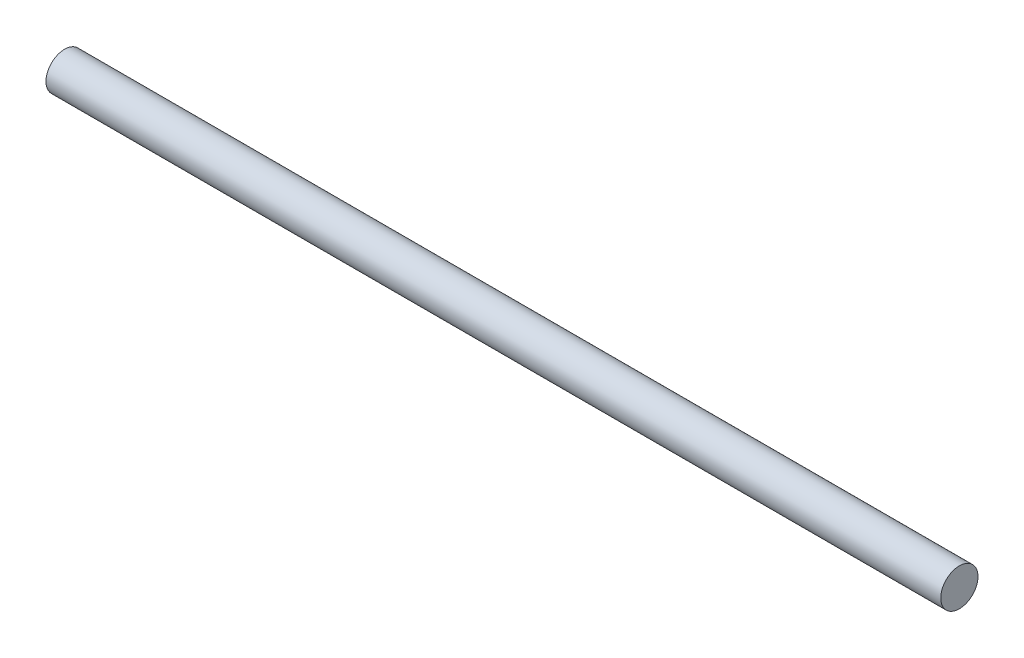
SolidWorks part; units mm, degrees
ref_plane "Front Plane" through (0, 0, 0) normal (0, 0, 1) x (1, 0, 0)
ref_plane "Top Plane" through (0, 0, 0) normal (0, 1, 0) x (1, 0, 0)
ref_plane "Right Plane" through (0, 0, 0) normal (1, 0, 0) x (0, 0, -1)
sketch "Sketch1" plane through (0, 0, 0) normal (1, 0, 0) x (0, 0, -1)
  circle A0 centre (0, 0) radius 3.175
  dimension "D1" = 6.35
extrude "Boss-Extrude1" add sketch "Sketch1" along normal blind 152.4
